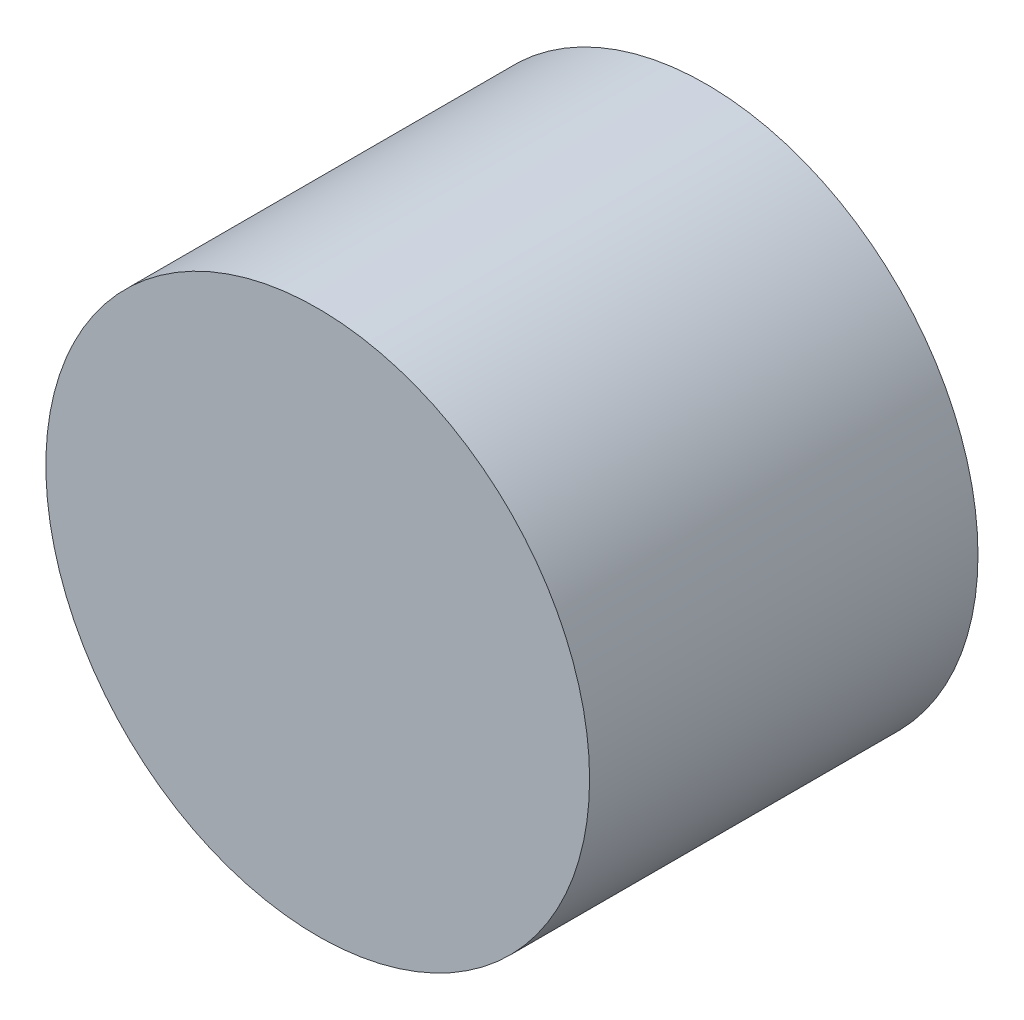
SolidWorks part; units mm, degrees
material "Caucho"
ref_plane "Alzado" through (0, 0, 0) normal (0, 0, 1) x (1, 0, 0)
ref_plane "Planta" through (0, 0, 0) normal (0, 1, 0) x (1, 0, 0)
ref_plane "Vista lateral" through (0, 0, 0) normal (1, 0, 0) x (0, 0, -1)
sketch "Croquis1" plane through (0, 0, 0) normal (0, 0, 1) x (1, 0, 0)
  circle A0 centre (-4.7541, 3.9783) radius 3.5
  dimension "D1" = 7
extrude "Saliente-Extruir1" add sketch "Croquis1" along normal blind 5
